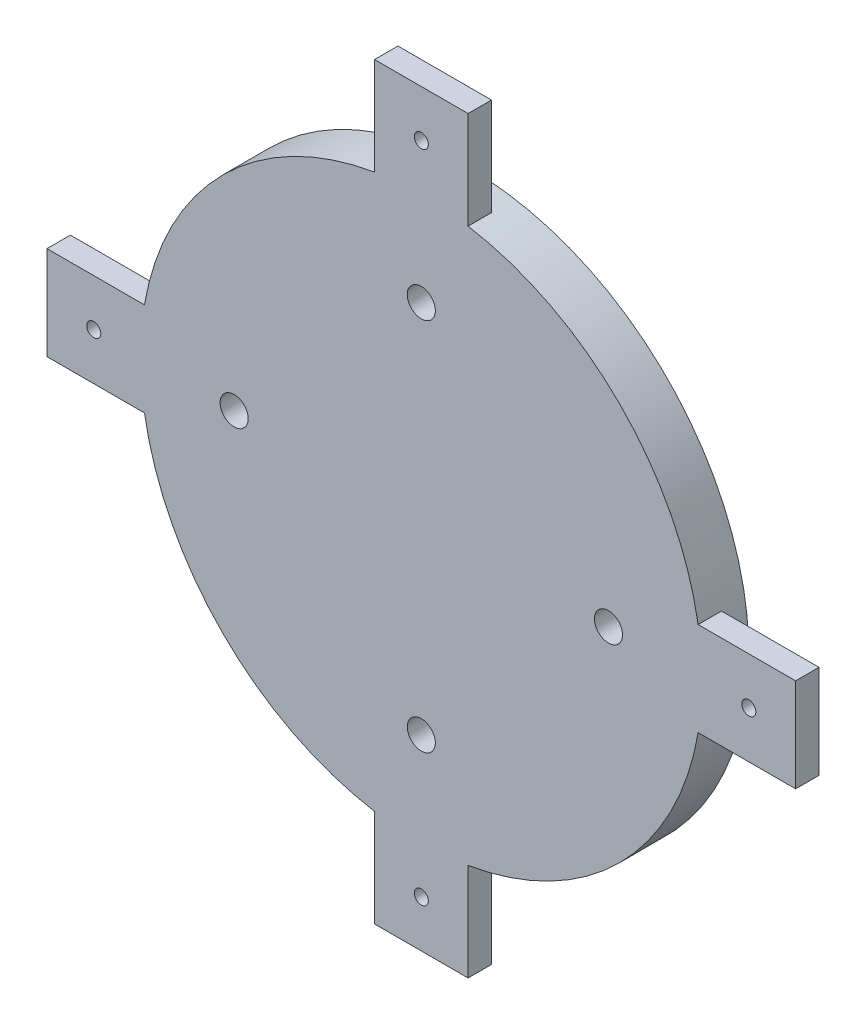
SolidWorks part; units mm, degrees
ref_plane "Front Plane" through (0, 0, 0) normal (0, 0, 1) x (1, 0, 0)
ref_plane "Top Plane" through (0, 0, 0) normal (0, 1, 0) x (1, 0, 0)
ref_plane "Right Plane" through (0, 0, 0) normal (1, 0, 0) x (0, 0, -1)
sketch "Sketch1" plane through (0, 0, 0) normal (0, 0, 1) x (1, 0, 0)
  circle A0 centre (0, 0) radius 60
extrude "Boss-Extrude1" add sketch "Sketch1" along normal blind 5
sketch "Sketch3" plane through (0, 0, 0) normal (0, 0, -1) x (-1, 0, 0)
  line L6 (10, -50) -> (-10, -50)
  line L7 (10, 50) -> (-10, 50)
  line L9 (50, 10) -> (80, 10)
  line L10 (50, 10) -> (50, -10)
  line L11 (50, -10) -> (80, -10)
  line L12 (80, 10) -> (80, -10)
  line L14 (10, 80) -> (-10, 80)
  line L15 (-10, 50) -> (-10, 80)
  line L16 (10, 50) -> (10, 80)
  line L21 (-10, -50) -> (-10, -80)
  line L22 (10, -80) -> (-10, -80)
  line L23 (10, -50) -> (10, -80)
  line L24 (-50, -10) -> (-80, -10)
  line L25 (-50, 10) -> (-50, -10)
  line L26 (-80, 10) -> (-80, -10)
  line L27 (-50, 10) -> (-80, 10)
extrude "Boss-Extrude2" add sketch "Sketch3" along normal blind 5
sketch "Sketch6" plane through (0, 0, 0) normal (0, 0, -1) x (-1, 0, 0)
  circle A0 centre (0, 0) radius 60
  dimension "D1" = 120
extrude "Boss-Extrude3" add sketch "Sketch6" along normal blind 10
sketch "Sketch7" plane through (0, 0, 5) normal (0, 0, 1) x (1, 0, 0)
  circle A0 centre (0, 0) radius 70
extrude "Cut-Extrude2" cut sketch "Sketch7" against normal blind 5
sketch "Sketch8" plane through (0, 0, 0) normal (0, 0, 1) x (1, 0, 0)
  circle A1 centre (0, -40) radius 3
  circle A2 centre (0, 40) radius 3
  circle A3 centre (-40, 0) radius 3
  circle A4 centre (40, 0) radius 3
  point P0 (0, 0)
extrude "Cut-Extrude7" cut sketch "Sketch8" against normal blind 5
sketch "Sketch13" plane through (0, 0, 0) normal (0, 0, 1) x (1, 0, 0)
  circle A1 centre (-40, 0) radius 1.5
  circle A2 centre (40, 0) radius 1.5
  circle A3 centre (-70, 0) radius 1.5
  circle A4 centre (70, 0) radius 1.5
  circle A5 centre (0, -40) radius 1.5
  circle A6 centre (0, -70) radius 1.5
  circle A7 centre (0, 40) radius 1.5
  circle A8 centre (0, 70) radius 1.5
  point P4 (0, 0)
extrude "Cut-Extrude10" cut sketch "Sketch13" against normal blind 10
